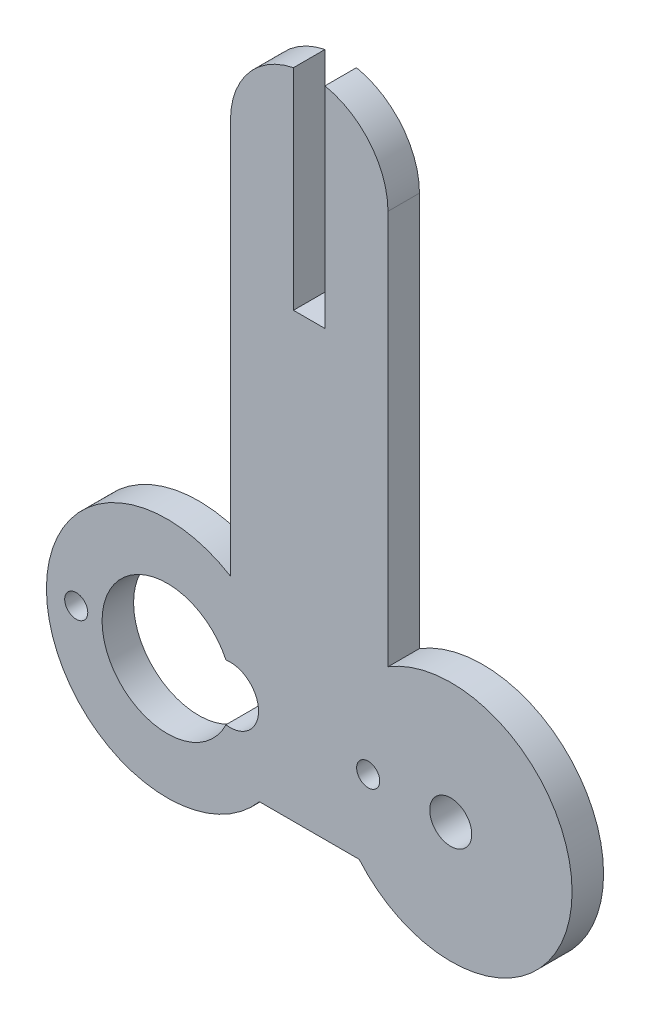
SolidWorks part; units mm, degrees
ref_plane "Front Plane" through (0, 0, 0) normal (0, 0, 1) x (1, 0, 0)
ref_plane "Top Plane" through (0, 0, 0) normal (0, 1, 0) x (1, 0, 0)
ref_plane "Right Plane" through (0, 0, 0) normal (1, 0, 0) x (0, 0, -1)
sketch "Model" plane through (0, 0, 0) normal (0, 0, 1) x (1, 0, 0)
  line L0 (36.0101, 56.158) -> (36.0101, 56.1561)
  line L1 (21.0101, 56.1288) -> (21.0101, 56.1269)
  line L2 (30.0101, 76.0529) -> (27.0101, 76.0529)
  line L3 (30.0101, 76.0529) -> (30.0101, 101.0529)
  line L4 (27.0101, 101.0529) -> (27.0101, 76.0529)
  line L5 (48.6459, 55.6974) -> (48.2061, 56.005)
  line L6 (48.2061, 56.005) -> (47.7295, 56.2862)
  line L7 (3.5394, 47.3443) -> (3.496, 46.7948)
  line L8 (47.2624, 56.5503) -> (46.7615, 56.7857)
  line L9 (3.5555, 45.1556) -> (3.6167, 44.6079)
  line L10 (46.2712, 57.0039) -> (45.7505, 57.1912)
  line L11 (49.918, 54.6592) -> (49.5023, 55.0245)
  line L12 (45.7505, 57.1912) -> (45.2416, 57.3615)
  line L13 (3.6167, 44.6079) -> (3.7197, 44.0724)
  line L14 (46.7615, 56.7857) -> (46.2712, 57.0039)
  line L15 (3.4952, 46.2496) -> (3.5042, 45.6985)
  line L16 (49.5023, 55.0245) -> (49.094, 55.3727)
  line L17 (3.5923, 47.887) -> (3.5394, 47.3443)
  line L18 (47.7295, 56.2862) -> (47.2624, 56.5503)
  line L19 (51.3456, 53.0148) -> (51.0054, 53.4511)
  line L20 (49.094, 55.3727) -> (48.6459, 55.6974)
  line L21 (3.7197, 44.0724) -> (3.8326, 43.5329)
  line L22 (3.6876, 48.4299) -> (3.5923, 47.887)
  line L23 (43.6363, 57.7069) -> (43.1041, 57.7772)
  line L24 (15.4851, 57.8156) -> (14.9342, 57.8314)
  line L25 (50.2912, 54.2734) -> (49.918, 54.6592)
  line L26 (3.496, 46.7948) -> (3.4952, 46.2496)
  line L27 (8.7862, 46.3327) -> (8.8373, 47.1266)
  line L28 (51.0054, 53.4511) -> (50.6708, 53.8709)
  line L29 (44.1827, 57.6201) -> (43.6363, 57.7069)
  line L30 (45.2416, 57.3615) -> (44.7057, 57.4992)
  line L31 (3.5042, 45.6985) -> (3.5555, 45.1556)
  line L32 (42.5519, 57.8124) -> (42.0156, 57.8315)
  line L33 (8.9895, 44.758) -> (8.8373, 45.5388)
  line L34 (8.8373, 47.1266) -> (8.9895, 47.9075)
  line L35 (38.7875, 57.3771) -> (38.2608, 57.2073)
  line L36 (3.8326, 43.5329) -> (3.9863, 43.0098)
  line L37 (13.2989, 57.7017) -> (12.7549, 57.6131)
  line L38 (50.6708, 53.8709) -> (50.2912, 54.2734)
  line L39 (16.5765, 57.7161) -> (16.0295, 57.784)
  line L40 (8.8373, 45.5388) -> (8.7862, 46.3327)
  line L41 (3.7921, 48.965) -> (3.6876, 48.4299)
  line L42 (15.651, 34.8635) -> (16.2011, 34.8971)
  line L43 (40.3776, 57.714) -> (39.8475, 57.6305)
  line L44 (52.1847, 51.6229) -> (51.9362, 52.0986)
  line L45 (44.7057, 57.4992) -> (44.1827, 57.6201)
  line L46 (14.9342, 57.8314) -> (14.3893, 57.8108)
  line L47 (43.1041, 57.7772) -> (42.5519, 57.8124)
  line L48 (42.0156, 57.8315) -> (41.4624, 57.8148)
  line L49 (16.7402, 34.9791) -> (17.2847, 35.0648)
  line L50 (39.3072, 57.5109) -> (38.7875, 57.3771)
  line L51 (14.0108, 34.8742) -> (14.5556, 34.8521)
  line L52 (39.8475, 57.6305) -> (39.3072, 57.5109)
  line L53 (18.1818, 57.3784) -> (17.6534, 57.513)
  line L54 (16.2011, 34.8971) -> (16.7402, 34.9791)
  line L55 (13.4642, 34.9451) -> (14.0108, 34.8742)
  line L56 (17.1153, 57.6326) -> (16.5765, 57.7161)
  line L57 (14.3893, 57.8108) -> (13.8393, 57.7742)
  line L58 (3.9863, 43.0098) -> (4.1499, 42.4834)
  line L59 (16.0295, 57.784) -> (15.4851, 57.8156)
  line L60 (12.7549, 57.6131) -> (12.2239, 57.4892)
  line L61 (13.8393, 57.7742) -> (13.2989, 57.7017)
  line L62 (37.7562, 57.0244) -> (37.2478, 56.8061)
  line L63 (41.4624, 57.8148) -> (40.9267, 57.7824)
  line L64 (51.9362, 52.0986) -> (51.6383, 52.5651)
  line L65 (51.6383, 52.5651) -> (51.3456, 53.0148)
  line L66 (19.7249, 56.8047) -> (19.2191, 57.0238)
  line L67 (15.1065, 34.8334) -> (15.651, 34.8635)
  line L68 (4.1499, 42.4834) -> (4.3529, 41.9773)
  line L69 (12.3866, 35.1417) -> (12.924, 35.0192)
  line L70 (4.2899, 50.5342) -> (4.0937, 50.0191)
  line L71 (12.2239, 57.4892) -> (11.6908, 57.3493)
  line L72 (12.924, 35.0192) -> (13.4642, 34.9451)
  line L73 (17.2847, 35.0648) -> (17.8134, 35.1979)
  line L74 (17.6534, 57.513) -> (17.1153, 57.6326)
  line L75 (40.9267, 57.7824) -> (40.3776, 57.714)
  line L76 (38.2608, 57.2073) -> (37.7562, 57.0244)
  line L77 (21.0101, 56.1269) -> (20.9062, 56.1883)
  line L78 (14.5556, 34.8521) -> (15.1065, 34.8334)
  line L79 (36.0921, 56.2048) -> (36.0101, 56.1561)
  line L80 (11.856, 35.2671) -> (12.3866, 35.1417)
  line L81 (4.0937, 50.0191) -> (3.9385, 49.4965)
  line L82 (4.7385, 51.5339) -> (4.4943, 51.0397)
  line L83 (40.4698, 43.5148) -> (39.9911, 43.8309)
  line L84 (20.9062, 56.1883) -> (20.7658, 56.2687)
  line L85 (8.2689, 55.6581) -> (7.8258, 55.3304)
  line L86 (38.8377, 45.7613) -> (38.7862, 46.3327)
  line L87 (38.8377, 46.9041) -> (38.9903, 47.4571)
  line L88 (4.3529, 41.9773) -> (4.5658, 41.4689)
  line L89 (18.7061, 57.2083) -> (18.1818, 57.3784)
  line L90 (7.4115, 54.9759) -> (7.0014, 54.6076)
  line L91 (17.8134, 35.1979) -> (18.3473, 35.3349)
  line L92 (10.1588, 56.7628) -> (9.6617, 56.5248)
  line L93 (37.2478, 56.8061) -> (36.811, 56.6001)
  line L94 (19.2191, 57.0238) -> (18.7061, 57.2083)
  line L95 (5.9103, 53.3827) -> (5.5772, 52.9436)
  line L96 (11.6908, 57.3493) -> (11.174, 57.1753)
  line L97 (39.2392, 44.6914) -> (38.9903, 45.2083)
  line L98 (22.5433, 48.5385) -> (22.9341, 48.2024)
  line L99 (7.0014, 54.6076) -> (6.6229, 54.2151)
  line L100 (11.174, 57.1753) -> (10.6566, 56.9855)
  line L101 (39.9911, 43.8309) -> (39.5764, 44.2273)
  line L102 (53.2582, 48.5467) -> (53.1546, 49.0745)
  line L103 (38.9903, 47.4571) -> (39.2392, 47.974)
  line L104 (22.9341, 44.463) -> (22.5433, 44.1269)
  line L105 (5.5772, 52.9436) -> (5.2803, 52.4862)
  line L106 (20.7658, 56.2687) -> (20.1793, 56.5918)
  line L107 (45.1733, 46.6196) -> (45.1733, 46.0459)
  line L108 (36.2198, 56.2778) -> (36.0921, 56.2048)
  line L109 (39.2392, 47.974) -> (39.5764, 48.4381)
  line L110 (43.7491, 43.6621) -> (43.2439, 43.3902)
  line L111 (9.6617, 56.5248) -> (9.1875, 56.2555)
  line L112 (52.4375, 51.1307) -> (52.1847, 51.6229)
  line L113 (21.0968, 43.635) -> (20.5821, 43.6631)
  line L114 (3.9385, 49.4965) -> (3.7921, 48.965)
  line L115 (23.6862, 46.3327) -> (23.637, 45.8196)
  line L116 (23.4912, 45.3251) -> (23.254, 44.8674)
  line L117 (22.0956, 43.8712) -> (21.6075, 43.7052)
  line L118 (36.811, 56.6001) -> (36.2198, 56.2778)
  line L119 (18.861, 35.5179) -> (19.3794, 35.705)
  line L120 (38.9903, 45.2083) -> (38.8377, 45.7613)
  line L121 (38.7862, 46.3327) -> (38.8377, 46.9041)
  line L122 (10.8164, 35.6155) -> (11.3326, 35.44)
  line L123 (6.015, 39.1535) -> (6.3622, 38.7254)
  line L124 (40.9974, 43.2893) -> (40.4698, 43.5148)
  line L125 (5.3719, 40.0404) -> (5.6769, 39.5813)
  line L126 (9.5862, 49.3789) -> (10.0207, 50.0453)
  line L127 (8.7152, 55.9714) -> (8.2689, 55.6581)
  line L128 (4.5658, 41.4689) -> (4.8162, 40.9845)
  line L129 (5.2803, 52.4862) -> (4.9903, 52.0175)
  line L130 (39.5764, 48.4381) -> (39.9911, 48.8346)
  line L131 (4.4943, 51.0397) -> (4.2899, 50.5342)
  line L132 (20.5821, 49.0023) -> (21.0968, 49.0305)
  line L133 (22.9341, 48.2024) -> (23.254, 47.7981)
  line L134 (14.8005, 40.1355) -> (14.0085, 40.2103)
  line L135 (9.2406, 44.0031) -> (8.9895, 44.758)
  line L136 (23.4912, 47.3404) -> (23.637, 46.8459)
  line L137 (40.9974, 49.3761) -> (41.5567, 49.5038)
  line L138 (22.6082, 37.7385) -> (23.0206, 38.1048)
  line L139 (10.6566, 56.9855) -> (10.1588, 56.7628)
  line L140 (35.9594, 94.5844) -> (35.808, 95.4433)
  line L141 (18.3473, 35.3349) -> (18.861, 35.5179)
  line L142 (19.7205, 50.3361) -> (20.1942, 49.6969)
  line L143 (44.0033, 35.011) -> (45.0682, 35.2534)
  line L144 (40.4698, 49.1506) -> (40.9974, 49.3761)
  line L145 (7.961, 37.2282) -> (8.4064, 36.9137)
  line L146 (14.0085, 40.2103) -> (13.2325, 40.3859)
  line L147 (38.6021, 35.3419) -> (39.6599, 35.0705)
  line L148 (21.3148, 36.7307) -> (21.7554, 37.0516)
  line L149 (44.1976, 44.0198) -> (43.7491, 43.6621)
  line L150 (8.86, 36.6005) -> (9.3334, 36.33)
  line L151 (19.8731, 35.9362) -> (20.3716, 36.1716)
  line L152 (21.0968, 49.0305) -> (21.6075, 48.9603)
  line L153 (35.5578, 96.2788) -> (35.2124, 97.0797)
  line L154 (14.8005, 52.5299) -> (15.5956, 52.5027)
  line L155 (44.5751, 44.4518) -> (44.1976, 44.0198)
  line L156 (7.1259, 37.9387) -> (7.5391, 37.583)
  line L157 (22.0956, 48.7943) -> (22.5433, 48.5385)
  line L158 (19.1689, 50.9093) -> (19.7205, 50.3361)
  line L159 (41.8288, 34.8338) -> (42.9202, 34.8707)
  line L160 (52.6392, 50.6335) -> (52.4375, 51.1307)
  line L161 (53.3632, 48.0103) -> (53.2582, 48.5467)
  line L162 (17.8693, 40.8438) -> (17.1427, 40.5199)
  line L163 (23.637, 46.8459) -> (23.6862, 46.3327)
  line L164 (22.2005, 37.3771) -> (22.6082, 37.7385)
  line L165 (41.5567, 49.5038) -> (42.1298, 49.5295)
  line L166 (23.254, 47.7981) -> (23.4912, 47.3404)
  line L167 (43.7491, 49.0034) -> (44.1976, 48.6457)
  line L168 (45.0709, 45.4814) -> (44.8693, 44.9443)
  line L169 (42.6983, 43.213) -> (42.1298, 43.1359)
  line L170 (23.0206, 38.1048) -> (23.2683, 38.3708)
  line L171 (16.3806, 52.3739) -> (17.1427, 52.1456)
  line L172 (44.8693, 47.7212) -> (45.0709, 47.184)
  line L173 (10.537, 50.6506) -> (11.1265, 51.1848)
  line L174 (42.1298, 49.5295) -> (42.6983, 49.4525)
  line L175 (11.7796, 41.0264) -> (11.1265, 41.4806)
  line L176 (12.4855, 52.006) -> (13.2325, 52.2795)
  line L177 (20.3716, 36.1716) -> (20.8409, 36.4491)
  line L178 (9.2406, 48.6624) -> (9.5862, 49.3789)
  line L179 (16.3806, 40.2916) -> (15.5956, 40.1627)
  line L180 (20.1942, 49.6969) -> (20.5821, 49.0023)
  line L181 (53.5151, 47.1396) -> (53.3632, 48.0103)
  line L182 (4.9903, 52.0175) -> (4.7385, 51.5339)
  line L183 (20.8409, 36.4491) -> (21.3148, 36.7307)
  line L184 (39.5764, 44.2273) -> (39.2392, 44.6914)
  line L185 (53.1546, 49.0745) -> (52.9981, 49.6053)
  line L186 (36.0101, 56.158) -> (36.0101, 93.7137)
  line L187 (12.4855, 40.6594) -> (11.7796, 41.0264)
  line L188 (49.094, 55.3727) -> (48.6459, 55.6974)
  line L189 (6.6229, 54.2151) -> (6.2496, 53.8096)
  line L190 (48.6459, 55.6974) -> (48.2061, 56.005)
  line L191 (6.7396, 38.3319) -> (7.1259, 37.9387)
  line L192 (47.7295, 56.2862) -> (47.2624, 56.5503)
  line L193 (5.6769, 39.5813) -> (6.015, 39.1535)
  line L194 (11.1265, 41.4806) -> (10.537, 42.0148)
  line L195 (49.918, 54.6592) -> (49.5023, 55.0245)
  line L196 (13.2325, 40.3859) -> (12.4855, 40.6594)
  line L197 (45.1733, 46.0459) -> (45.0709, 45.4814)
  line L198 (23.637, 45.8196) -> (23.4912, 45.3251)
  line L199 (7.5391, 37.583) -> (7.961, 37.2282)
  line L200 (42.1298, 43.1359) -> (41.5567, 43.1617)
  line L201 (10.0207, 50.0453) -> (10.537, 50.6506)
  line L202 (5.0763, 40.4986) -> (5.3719, 40.0404)
  line L203 (10.3117, 35.8373) -> (10.8164, 35.6155)
  line L204 (23.254, 44.8674) -> (22.9341, 44.463)
  line L205 (19.3794, 35.705) -> (19.8731, 35.9362)
  line L206 (6.2496, 53.8096) -> (5.9103, 53.3827)
  line L207 (45.0709, 47.184) -> (45.1733, 46.6196)
  line L208 (21.6075, 43.7052) -> (21.0968, 43.635)
  line L209 (21.7554, 37.0516) -> (22.2005, 37.3771)
  line L210 (9.3334, 36.33) -> (9.8147, 36.0613)
  line L211 (9.1875, 56.2555) -> (8.7152, 55.9714)
  line L212 (39.9911, 48.8346) -> (40.4698, 49.1506)
  line L213 (7.8258, 55.3304) -> (7.4115, 54.9759)
  line L214 (8.4064, 36.9137) -> (8.86, 36.6005)
  line L215 (4.8162, 40.9845) -> (5.0763, 40.4986)
  line L216 (6.3622, 38.7254) -> (6.7396, 38.3319)
  line L217 (36.0101, 93.7137) -> (35.9594, 94.5844)
  line L218 (10.0207, 42.6201) -> (9.5862, 43.2865)
  line L219 (9.5862, 43.2865) -> (9.2406, 44.0031)
  line L220 (10.537, 42.0148) -> (10.0207, 42.6201)
  line L221 (9.8147, 36.0613) -> (10.3117, 35.8373)
  line L222 (52.9981, 49.6053) -> (52.8448, 50.1196)
  line L223 (35.808, 95.4433) -> (35.5578, 96.2788)
  line L224 (17.1427, 52.1456) -> (17.8693, 51.8216)
  line L225 (44.5751, 48.2136) -> (44.8693, 47.7212)
  line L226 (37.5748, 35.7125) -> (38.6021, 35.3419)
  line L227 (18.5484, 41.2582) -> (17.8693, 40.8438)
  line L228 (52.7911, 42.3951) -> (53.1159, 43.4378)
  line L229 (11.7796, 51.6391) -> (12.4855, 52.006)
  line L230 (34.2555, 98.5346) -> (33.6569, 99.169)
  line L231 (15.5956, 52.5027) -> (16.3806, 52.3739)
  line L232 (31.4807, 100.6003) -> (30.6612, 100.8986)
  line L233 (46.1052, 35.5957) -> (47.1052, 36.0348)
  line L234 (53.1159, 43.4378) -> (53.3403, 44.5066)
  line L235 (22.244, 97.835) -> (21.8079, 97.0797)
  line L236 (50.5597, 38.6682) -> (51.2481, 39.516)
  line L237 (48.9579, 37.1869) -> (49.794, 37.8895)
  line L238 (21.2123, 95.4433) -> (21.0608, 94.5844)
  line L239 (21.8079, 97.0797) -> (21.4624, 96.2788)
  line L240 (21.0608, 94.5844) -> (21.0101, 93.7137)
  line L241 (22.7648, 98.5346) -> (22.244, 97.835)
  line L242 (43.2439, 49.2752) -> (43.7491, 49.0034)
  line L243 (24.7601, 100.2089) -> (24.0314, 99.7296)
  line L244 (19.1689, 41.7561) -> (18.5484, 41.2582)
  line L245 (24.0314, 99.7296) -> (23.3633, 99.169)
  line L246 (49.794, 37.8895) -> (50.5597, 38.6682)
  line L247 (26.3591, 100.8986) -> (25.5395, 100.6003)
  line L248 (32.2601, 100.2089) -> (31.4807, 100.6003)
  line L249 (33.9502, 38.1065) -> (34.7667, 37.3813)
  line L250 (52.3688, 41.3879) -> (52.7911, 42.3951)
  line L251 (35.6484, 36.7368) -> (36.5872, 36.1789)
  line L252 (53.3403, 44.5066) -> (53.5036, 45.3752)
  line L253 (34.7667, 37.3813) -> (35.6484, 36.7368)
  line L254 (36.5872, 36.1789) -> (37.5748, 35.7125)
  line L255 (33.2061, 38.9058) -> (33.9502, 38.1065)
  line L256 (51.853, 40.4253) -> (52.3688, 41.3879)
  line L257 (36.0101, 56.158) -> (36.0101, 93.7137)
  line L258 (23.3633, 99.169) -> (22.7648, 98.5346)
  line L259 (21.0101, 93.7137) -> (21.0101, 56.1288)
  line L260 (27.0101, 101.0529) -> (26.3591, 100.8986)
  line L261 (23.7664, 38.9058) -> (33.2061, 38.9058)
  line L262 (53.5621, 46.2571) -> (53.5151, 47.1396)
  line L263 (47.2624, 56.5503) -> (46.7615, 56.7857)
  line L264 (50.2912, 54.2734) -> (49.918, 54.6592)
  line L265 (45.7505, 57.1912) -> (45.2416, 57.3615)
  line L266 (48.2061, 56.005) -> (47.7295, 56.2862)
  line L267 (46.7615, 56.7857) -> (46.2712, 57.0039)
  line L268 (46.2712, 57.0039) -> (45.7505, 57.1912)
  line L269 (49.5023, 55.0245) -> (49.094, 55.3727)
  line L270 (33.6569, 99.169) -> (32.9888, 99.7296)
  line L271 (23.2683, 38.3708) -> (23.7664, 38.9058)
  line L272 (25.5395, 100.6003) -> (24.7601, 100.2089)
  line L273 (32.9888, 99.7296) -> (32.2601, 100.2089)
  line L274 (47.1052, 36.0348) -> (48.0589, 36.5668)
  line L275 (20.1942, 42.9686) -> (19.7205, 42.3294)
  line L276 (34.7763, 97.835) -> (34.2555, 98.5346)
  line L277 (51.2481, 39.516) -> (51.853, 40.4253)
  line L278 (53.5036, 45.3752) -> (53.5621, 46.2571)
  line L279 (45.0682, 35.2534) -> (46.1052, 35.5957)
  line L280 (14.0085, 52.4551) -> (14.8005, 52.5299)
  line L281 (35.2124, 97.0797) -> (34.7763, 97.835)
  line L282 (42.6983, 49.4525) -> (43.2439, 49.2752)
  line L283 (48.0589, 36.5668) -> (48.9579, 37.1869)
  line L284 (15.5956, 40.1627) -> (14.8005, 40.1355)
  line L285 (30.6612, 100.8986) -> (30.0101, 101.0529)
  line L286 (42.9202, 34.8707) -> (44.0033, 35.011)
  line L287 (44.1976, 48.6457) -> (44.5751, 48.2136)
  line L288 (21.4624, 96.2788) -> (21.2123, 95.4433)
  line L289 (40.7387, 34.9006) -> (41.8288, 34.8338)
  line L290 (17.8693, 51.8216) -> (18.5484, 51.4072)
  line L291 (17.1427, 40.5199) -> (16.3806, 40.2916)
  line L292 (18.5484, 51.4072) -> (19.1689, 50.9093)
  line L293 (13.2325, 52.2795) -> (14.0085, 52.4551)
  line L294 (39.6599, 35.0705) -> (40.7387, 34.9006)
  line L295 (19.7205, 42.3294) -> (19.1689, 41.7561)
  line L296 (11.1265, 51.1848) -> (11.7796, 51.6391)
  line L297 (44.8693, 44.9443) -> (44.5751, 44.4518)
  line L298 (20.5821, 43.6631) -> (20.1942, 42.9686)
  line L299 (52.8448, 50.1196) -> (52.6392, 50.6335)
  line L300 (11.3326, 35.44) -> (11.856, 35.2671)
  line L301 (21.6075, 48.9603) -> (22.0956, 48.7943)
  line L302 (8.9895, 47.9075) -> (9.2406, 48.6624)
  line L303 (20.1793, 56.5918) -> (19.7249, 56.8047)
  line L304 (41.5567, 43.1617) -> (40.9974, 43.2893)
  line L305 (43.2439, 43.3902) -> (42.6983, 43.213)
  line L306 (22.5433, 44.1269) -> (22.0956, 43.8712)
  circle A0 centre (6.3262, 46.3327) radius 1.1
  circle A1 centre (34.1262, 46.3327) radius 1.1
sketch "Sketch2" plane through (0, 0, 0) normal (0, 0, 1) x (1, 0, 0)
  circle A0 centre (41.9862, 46.3327) radius 3.2
sketch "Sketch3" plane through (0, 0, 0) normal (0, 0, 1) x (1, 0, 0)
  line L0 (23.7664, 38.9058) -> (33.2061, 38.9058)
  line L1 (27.0101, 81.0529) -> (27.0101, 101.0529)
  line L3 (30.0101, 81.0529) -> (30.0101, 101.0529)
  line L4 (36.0101, 93.7137) -> (36.0101, 56.158)
  line L5 (21.0101, 56.1288) -> (21.0101, 93.7137)
  line L6 (30.0101, 101.0529) -> (30.0101, 101.0622)
  line L7 (27.0101, 101.0529) -> (27.0101, 101.0622)
  line L8 (33.2061, 38.9058) -> (33.2647, 38.9058)
  line L9 (21.0101, 56.1288) -> (21.0101, 56.1278)
  line L10 (21.0101, 56.1278) -> (21.0101, 56.1268)
  line L11 (36.0101, 56.158) -> (36.0101, 56.1531)
  line L13 (27.0101, 81.0529) -> (30.0101, 81.0529)
  arc A1 (20.5821, 49.0023) -> (20.5821, 43.6631) centre (14.9862, 46.3327) ccw
  arc A2 (20.5821, 43.6631) -> (20.5821, 49.0023) centre (20.9862, 46.3327) ccw
  arc A3 (21.0101, 56.1278) -> (23.7664, 38.9058) centre (14.9864, 46.3322) ccw
  arc A4 (33.2647, 38.9058) -> (36.0101, 56.1549) centre (42.0359, 46.3528) ccw
  arc A5 (36.0101, 93.7137) -> (30.0101, 101.0622) centre (28.5101, 93.7137) ccw
  arc A6 (27.0101, 101.0622) -> (21.0101, 93.7137) centre (28.5101, 93.7137) ccw
  circle A7 centre (6.3262, 46.3327) radius 1.1
  circle A8 centre (34.1262, 46.3327) radius 1.1
  point P0 (41.9862, 46.3327)
  dimension "D2" = 11.5062
  dimension "D4" = 6.2
  dimension "D5" = 2.7
  dimension "D6" = 2.2
  dimension "D7" = 2.2
  dimension "D3" = 27
  dimension "D8" = 7.86
  dimension "D9" = 6
  dimension "D10" = 8.66
extrude "Boss-Extrude1" add sketch "Sketch3" along normal blind 3
sketch "Sketch5" plane through (0, 0, 3) normal (0, 0, 1) x (1, 0, 0)
  circle A0 centre (41.9862, 46.3327) radius 2
extrude "Cut-Extrude1" cut sketch "Sketch5" against normal blind 3 contours A0
